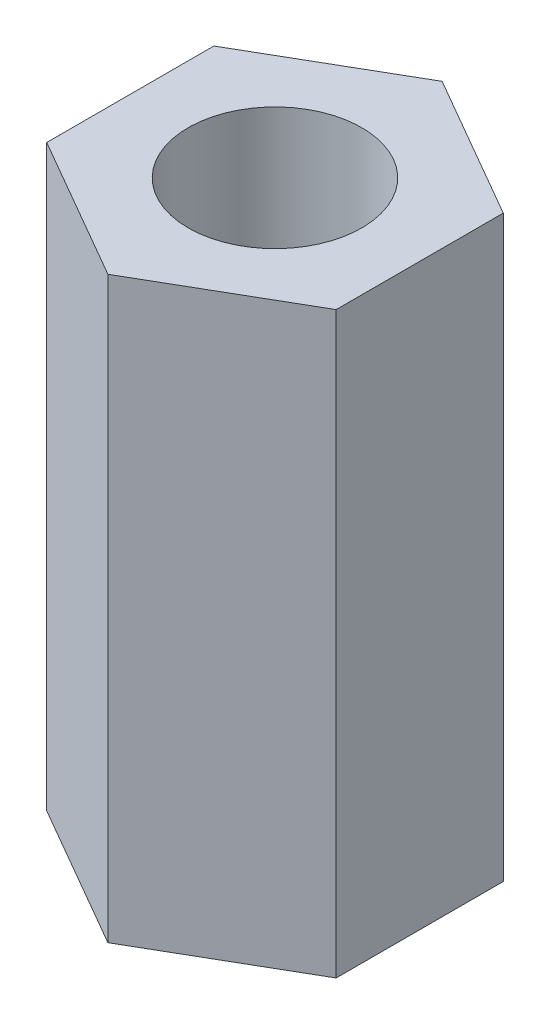
SolidWorks part; units mm, degrees
ref_plane "Piano frontale" through (0, 0, 0) normal (0, 0, 1) x (1, 0, 0)
ref_plane "Piano superiore" through (0, 0, 0) normal (0, 1, 0) x (1, 0, 0)
ref_plane "Piano destro" through (0, 0, 0) normal (1, 0, 0) x (0, 0, -1)
sketch "Sketch1" plane through (0, 0, 0) normal (0, 1, 0) x (1, 0, 0)
  line L1 (-34.9518, 17.0938) -> (-37.4518, 15.6504)
  line L2 (-37.4518, 15.6504) -> (-37.4518, 12.7637)
  line L3 (-37.4518, 12.7637) -> (-34.9518, 11.3203)
  line L4 (-34.9518, 11.3203) -> (-32.4518, 12.7637)
  line L5 (-32.4518, 12.7637) -> (-32.4518, 15.6504)
  line L6 (-32.4518, 15.6504) -> (-34.9518, 17.0938)
  circle A0 centre (-34.9518, 14.207) radius 2.5 construction
  circle A1 centre (-34.9518, 14.207) radius 1.5
  dimension "D1" = 3
  dimension "D2" = 5
extrude "Boss-Extrude1" add sketch "Sketch1" along normal blind 10
